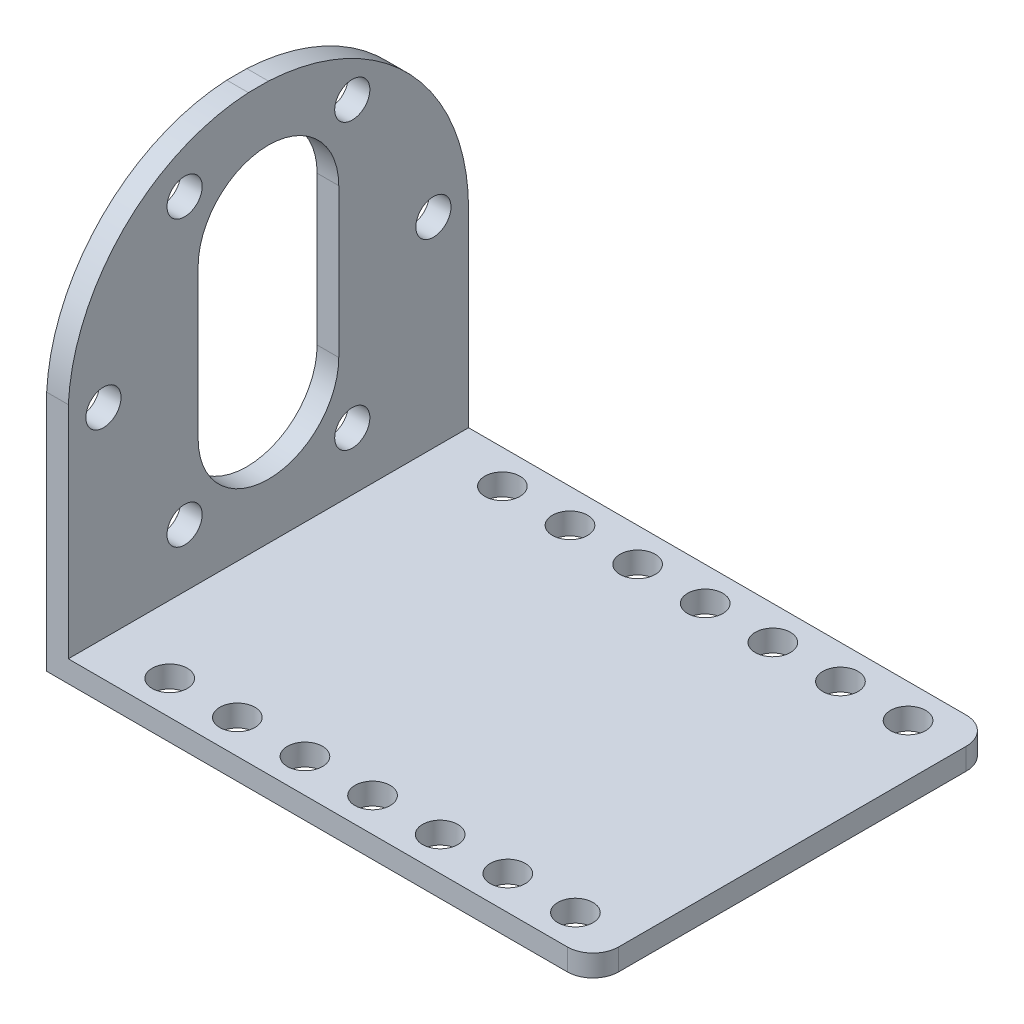
SolidWorks part; units mm, degrees
material "6061 Alloy"
ref_plane "Front Plane" through (0, 0, 0) normal (0, 0, 1) x (1, 0, 0)
ref_plane "Top Plane" through (0, 0, 0) normal (0, 1, 0) x (1, 0, 0)
ref_plane "Right Plane" through (0, 0, 0) normal (1, 0, 0) x (0, 0, -1)
sketch "Sketch1" plane through (0, 0, 0) normal (0, 0, 1) x (1, 0, 0)
  line L1 (-1.016, 18.796) -> (1.016, 18.796)
  line L2 (-1.016, 18.796) -> (-1.016, -18.796)
  line L4 (1.016, 18.796) -> (1.016, -18.796)
  line L5 (-1.016, 18.796) -> (1.016, -18.796) construction
  line L6 (-1.016, -18.796) -> (1.016, 18.796) construction
  line L7 (1.016, -18.796) -> (50.292, -18.796)
  line L8 (-1.016, -18.796) -> (-1.016, -20.828)
  line L9 (-1.016, -20.828) -> (50.292, -20.828)
  line L10 (50.292, -18.796) -> (50.292, -20.828)
  point P0 (0, 0)
  dimension "D1" = 37.592
  dimension "D2" = 2.032
  dimension "D3" = 2.032
  dimension "D4" = 51.308
extrude "Boss-Extrude1" add sketch "Sketch1" against normal blind 37.592
sketch "Sketch2" plane through (-1.016, 0, 0) normal (-1, 0, 0) x (0, 0, 1)
  line L0 (-37.592, -20.828) -> (0, -20.828) construction
  line L2 (-25.4, -6.985) -> (-25.4, 6.985)
  line L4 (-12.192, -6.985) -> (-12.192, 6.985)
  arc A0 (-25.4, 6.985) -> (-12.192, 6.985) centre (-18.796, 6.985) cw
  arc A1 (-25.4, -6.985) -> (-12.192, -6.985) centre (-18.796, -6.985) ccw
  point P7 (-18.796, -6.985)
  point P8 (-12.192, 0)
  point P10 (-18.796, -20.828)
  dimension "D1" = 13.208
  dimension "D2" = 13.97
  dimension "D3" = 20.828
  dimension "D4" = 0
extrude "Cut-Extrude1" cut sketch "Sketch2" against normal blind 37.592
sketch "Sketch3" plane through (-1.016, 0, 0) normal (-1, 0, 0) x (0, 0, 1)
  line L0 (-37.592, -20.828) -> (0, -20.828) construction
  circle A0 centre (-18.796, 0) radius 15.494
  circle A1 centre (-34.29, 0) radius 1.651
  circle A2 centre (-26.67, -13.3441) radius 1.651
  circle A3 centre (-10.922, -13.3441) radius 1.651
  circle A4 centre (-3.302, 0) radius 1.651
  circle A5 centre (-10.922, 13.3441) radius 1.651
  circle A6 centre (-26.67, 13.3441) radius 1.651
  point P2 (-18.796, -20.828)
  dimension "D1" = 30.988
  dimension "D2" = 3.302
  dimension "D3" = 3.302
  dimension "D4" = 3.302
  dimension "D5" = 3.302
  dimension "D6" = 3.302
  dimension "D7" = 3.302
  dimension "D8" = 7.874
extrude "Cut-Extrude3" cut sketch "Sketch3" against normal blind 37.592 contours A6 | A1 | A2 | A3 | A4 | A5
sketch "Sketch5" plane through (-1.016, 0, 0) normal (-1, 0, 0) x (0, 0, 1)
  line L0 (-37.592, 18.796) -> (0, 18.796) construction
  line L1 (-37.592, 18.796) -> (-37.592, -20.828) construction
  line L2 (-37.592, -1.016) -> (-37.592, 18.796)
  line L3 (-37.592, 18.796) -> (0, 18.796)
  arc A0 (-37.592, -1.016) -> (-18.796, 18.796) centre (-17.7525, -1.016) cw
  arc A1 (-18.796, 18.796) -> (0, 0) centre (-17.8556, 0.9404) cw
  point P0 (-18.796, 18.796)
  point P1 (0, 0)
  point P4 (-37.592, -1.016)
  line M11 (0, -20.828) -> (0, 18.796)
  line M12 (0, 18.796) -> (-37.592, 18.796)
  line M13 (-37.592, 18.796) -> (-37.592, -20.828)
extrude "Cut-Extrude4" cut sketch "Sketch5" against normal blind 37.592 contours A0 L3 M13 | A1 M12 M11
sketch "Sketch6" plane through (0, -18.796, 0) normal (0, 1, 0) x (1, 0, 0)
  line L0 (50.292, 2.413) -> (50.292, 0)
  line L1 (50.292, 37.592) -> (50.292, 0) construction
  line L2 (50.292, 0) -> (47.879, 0)
  line L3 (50.292, 0) -> (1.016, 0) construction
  arc A0 (50.292, 2.413) -> (47.879, 0) centre (47.879, 2.413) cw
  dimension "D1" = 2.413
  dimension "D2" = 2.413
extrude "Cut-Extrude5" cut sketch "Sketch6" against normal blind 37.592
sketch "Sketch7" plane through (0, -18.796, 0) normal (0, 1, 0) x (1, 0, 0)
  line L0 (50.292, 37.592) -> (50.292, 2.413) construction
  line L2 (47.879, 0) -> (1.016, 0) construction
  circle A0 centre (45.466, 3.175) radius 1.651
  circle A1 centre (45.466, 34.417) radius 1.651
  dimension "D1" = 3.302
  dimension "D3" = 3.302
  dimension "D4" = 4.826
  dimension "D6" = 3.175
  dimension "D2" = 4.826
  dimension "D5" = 31.242
extrude "Cut-Extrude6" cut sketch "Sketch7" against normal blind 37.592
pattern_linear "LPattern1" count 7 spacing 6.35 along (-1, 0, 0) of "Cut-Extrude6"
sketch "Sketch8" plane through (0, -18.796, 0) normal (0, 1, 0) x (1, 0, 0)
  line L0 (50.292, 35.052) -> (50.292, 37.592)
  line L1 (50.292, 37.592) -> (50.292, 2.413) construction
  line L2 (50.292, 37.592) -> (47.752, 37.592)
  line L3 (50.292, 37.592) -> (1.016, 37.592) construction
  arc A0 (47.752, 37.592) -> (50.292, 35.052) centre (47.752, 35.052) cw
  dimension "D1" = 2.54
  dimension "D2" = 2.54
extrude "Cut-Extrude7" cut sketch "Sketch8" against normal blind 37.592
